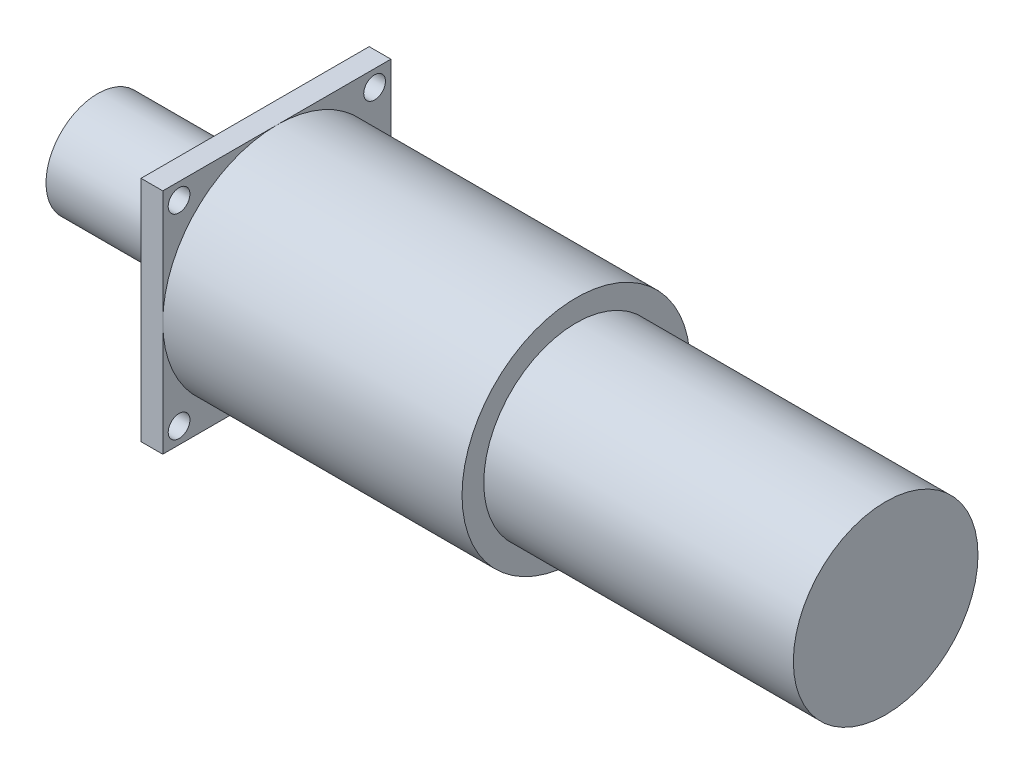
SolidWorks part; units mm, degrees
ref_plane "Plano frontal" through (0, 0, 0) normal (0, 0, 1) x (1, 0, 0)
ref_plane "Plano superior" through (0, 0, 0) normal (0, 1, 0) x (1, 0, 0)
ref_plane "Plano direito" through (0, 0, 0) normal (1, 0, 0) x (0, 0, -1)
sketch "Esboço1" plane through (0, 0, 0) normal (0, 0, 1) x (1, 0, 0)
  line L0 (0, 0) -> (112.9728, 0) construction
  line L1 (-29, 0) -> (-29, 9.5)
  line L2 (-29, 9.5) -> (-11.2, 9.5)
  line L3 (-11.2, 9.5) -> (-11.2, 4)
  line L4 (0, 15) -> (-3.7, 15)
  line L5 (0, 15) -> (0, 21)
  line L6 (0, 21) -> (59.1, 21)
  line L7 (59.1, 21) -> (59.1, 17)
  line L8 (59.1, 17) -> (116.1, 17)
  line L9 (116.1, 17) -> (116.1, 0)
  line L10 (-3.7, 15) -> (-3.7, 4)
  line L11 (-3.7, 4) -> (-11.2, 4)
  line L12 (-29, 0) -> (116.1, 0)
  point P18 (-7.45, 4)
  dimension "D1" = 34
  dimension "D2" = 42
  dimension "D3" = 57
  dimension "D4" = 59.1
  dimension "D5" = 3.7
  dimension "D6" = 17.8
  dimension "D7" = 19
  dimension "D8" = 25.3
  dimension "D9" = 30
  dimension "D10" = 8
revolve "Revolução1" add sketch "Esboço1" angle 360 about L0
sketch "Esboço2" plane through (0, 0, 0) normal (-1, 0, 0) x (0, 0, 1)
  line L1 (-21, 21) -> (21, 21)
  line L2 (-21, 21) -> (-21, -21)
  line L3 (-21, -21) -> (21, -21)
  line L4 (21, 21) -> (21, -21)
  line L5 (-21, 21) -> (21, -21) construction
  line L6 (-21, -21) -> (21, 21) construction
  circle A0 centre (0, 0) radius 21 construction
  point P0 (0, 0)
extrude "Ressalto-extrusão1" add sketch "Esboço2" against normal blind 4
sketch "Esboço3" plane through (4, 0, 0) normal (1, 0, 0) x (0, 0, -1)
  line L0 (0, 0) -> (0, -6.433) construction
  line L1 (0, 0) -> (-7.3877, 0) construction
  line L2 (0, 0) -> (-18, 18) construction
  line L3 (-20, 18) -> (-21, 18) construction
  line L4 (-21, 0) -> (-21, 21) construction
  circle A0 centre (-18, 18) radius 2
  circle A1 centre (-18, -18) radius 2
  circle A2 centre (18, -18) radius 2
  circle A3 centre (18, 18) radius 2
  dimension "D1" = 4
  dimension "D2" = 45
  dimension "D3" = 1
extrude "Corte-extrusão1" cut sketch "Esboço3" against normal blind 4
